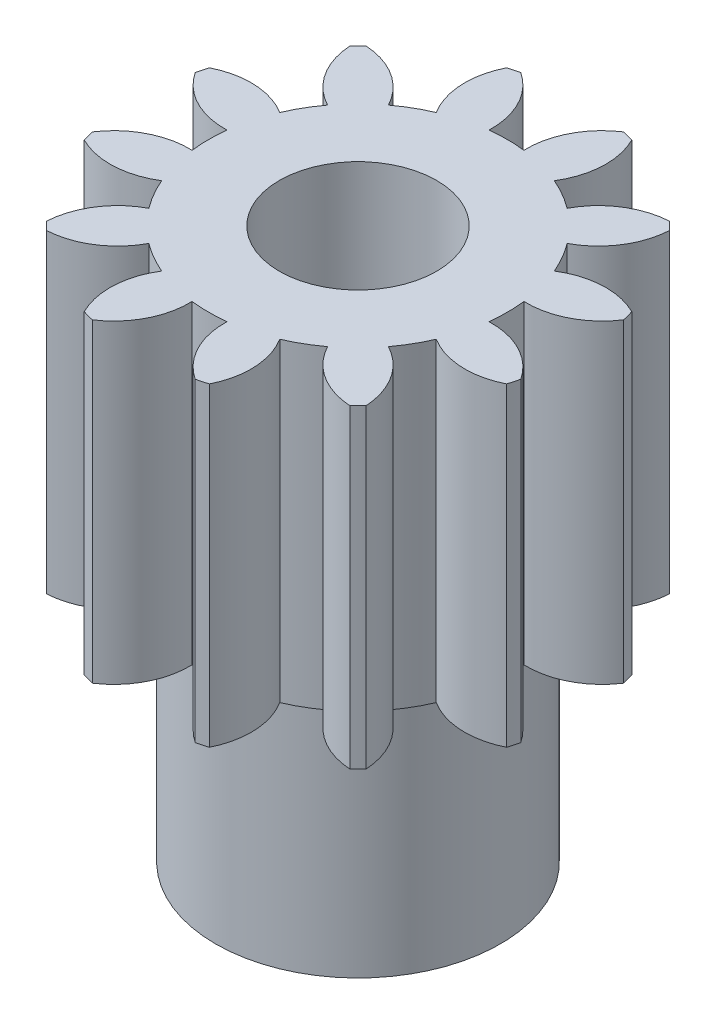
SolidWorks part; units mm, degrees
ref_plane "Front Plane" through (0, 0, 0) normal (0, 0, 1) x (1, 0, 0)
ref_plane "Top Plane" through (0, 0, 0) normal (0, 1, 0) x (1, 0, 0)
ref_plane "Right Plane" through (0, 0, 0) normal (1, 0, 0) x (0, 0, -1)
sketch "Sketch1" plane through (0, 0, 0) normal (0, 1, 0) x (1, 0, 0)
  circle A0 centre (0, 0) radius 17
  dimension "D1" = 34
extrude "Boss-Extrude1" add sketch "Sketch1" along normal blind 20
extrude "Cut-Extrude1" cut sketch "Sketch2" against normal blind 15
sketch "Sketch2" plane through (-13.8182, 15, -17.4966) normal (0, 1, 0) x (1, 0, 0)
  circle A0 centre (13.8182, -17.4966) radius 17
  arc A96 (19.498, -25.1104) -> (23.4557, -27.6513) centre (23.7376, -22.8596) ccw
  arc A97 (23.4557, -27.6513) -> (23.973, -27.1341) centre (13.8182, -17.4966) ccw
  arc A98 (23.973, -27.1341) -> (21.4321, -23.1764) centre (19.1813, -27.4159) ccw
  arc A99 (21.4321, -23.1764) -> (22.544, -21.2505) centre (13.8182, -17.4966) ccw
  arc A100 (22.544, -21.2505) -> (27.2419, -21.4721) centre (25.0902, -17.1814) ccw
  arc A101 (27.2419, -21.4721) -> (27.4313, -20.7655) centre (13.8182, -17.4966) ccw
  arc A102 (27.4313, -20.7655) -> (23.2519, -18.6085) centre (23.4224, -23.4055) ccw
  arc A103 (23.2519, -18.6085) -> (23.2519, -16.3847) centre (13.8182, -17.4966) ccw
  arc A104 (23.2519, -16.3847) -> (27.4313, -14.2276) centre (23.4224, -11.5877) ccw
  arc A105 (27.4313, -14.2276) -> (27.2419, -13.5211) centre (13.8182, -17.4966) ccw
  arc A106 (27.2419, -13.5211) -> (22.544, -13.7427) centre (25.0902, -17.8117) ccw
  arc A107 (22.544, -13.7427) -> (21.4321, -11.8168) centre (13.8182, -17.4966) ccw
  arc A108 (21.4321, -11.8168) -> (23.973, -7.8591) centre (19.1813, -7.5772) ccw
  arc A109 (23.973, -7.8591) -> (23.4557, -7.3418) centre (13.8182, -17.4966) ccw
  arc A110 (23.4557, -7.3418) -> (19.498, -9.8827) centre (23.7376, -12.1336) ccw
  arc A111 (19.498, -9.8827) -> (17.5722, -8.7708) centre (13.8182, -17.4966) ccw
  arc A112 (17.5722, -8.7708) -> (17.7938, -4.0729) centre (13.5031, -6.2247) ccw
  arc A113 (17.7938, -4.0729) -> (17.0872, -3.8836) centre (13.8182, -17.4966) ccw
  arc A114 (17.0872, -3.8836) -> (14.9302, -8.0629) centre (19.7271, -7.8924) ccw
  arc A115 (14.9302, -8.0629) -> (12.7063, -8.0629) centre (13.8182, -17.4966) ccw
  arc A116 (12.7063, -8.0629) -> (10.5493, -3.8836) centre (7.9094, -7.8924) ccw
  arc A117 (10.5493, -3.8836) -> (9.8427, -4.0729) centre (13.8182, -17.4966) ccw
  arc A118 (9.8427, -4.0729) -> (10.0643, -8.7708) centre (14.1334, -6.2247) ccw
  arc A119 (10.0643, -8.7708) -> (8.1385, -9.8827) centre (13.8182, -17.4966) ccw
  arc A120 (8.1385, -9.8827) -> (4.1808, -7.3418) centre (3.8989, -12.1336) ccw
  arc A121 (4.1808, -7.3418) -> (3.6635, -7.8591) centre (13.8182, -17.4966) ccw
  arc A122 (3.6635, -7.8591) -> (6.2044, -11.8168) centre (8.4552, -7.5772) ccw
  arc A123 (6.2044, -11.8168) -> (5.0925, -13.7427) centre (13.8182, -17.4966) ccw
  arc A124 (5.0925, -13.7427) -> (0.3946, -13.5211) centre (2.5463, -17.8117) ccw
  arc A125 (0.3946, -13.5211) -> (0.2052, -14.2276) centre (13.8182, -17.4966) ccw
  arc A126 (0.2052, -14.2276) -> (4.3845, -16.3847) centre (4.2141, -11.5877) ccw
  arc A127 (4.3845, -16.3847) -> (4.3845, -18.6085) centre (13.8182, -17.4966) ccw
  arc A128 (4.3845, -18.6085) -> (0.2052, -20.7655) centre (4.2141, -23.4055) ccw
  arc A129 (0.2052, -20.7655) -> (0.3946, -21.4721) centre (13.8182, -17.4966) ccw
  arc A130 (0.3946, -21.4721) -> (5.0925, -21.2505) centre (2.5463, -17.1814) ccw
  arc A131 (5.0925, -21.2505) -> (6.2044, -23.1764) centre (13.8182, -17.4966) ccw
  arc A132 (6.2044, -23.1764) -> (3.6635, -27.1341) centre (8.4552, -27.4159) ccw
  arc A133 (3.6635, -27.1341) -> (4.1808, -27.6513) centre (13.8182, -17.4966) ccw
  arc A134 (4.1808, -27.6513) -> (8.1385, -25.1104) centre (3.8989, -22.8596) ccw
  arc A135 (8.1385, -25.1104) -> (10.0643, -26.2224) centre (13.8182, -17.4966) ccw
  arc A136 (10.0643, -26.2224) -> (9.8427, -30.9203) centre (14.1334, -28.7685) ccw
  arc A137 (9.8427, -30.9203) -> (10.5493, -31.1096) centre (13.8182, -17.4966) ccw
  arc A138 (10.5493, -31.1096) -> (12.7063, -26.9303) centre (7.9094, -27.1008) ccw
  arc A139 (12.7063, -26.9303) -> (14.9302, -26.9303) centre (13.8182, -17.4966) ccw
  arc A140 (14.9302, -26.9303) -> (17.0872, -31.1096) centre (19.7271, -27.1008) ccw
  arc A141 (17.0872, -31.1096) -> (17.7938, -30.9203) centre (13.8182, -17.4966) ccw
  arc A142 (17.7938, -30.9203) -> (17.5722, -26.2224) centre (13.5031, -28.7685) ccw
  arc A143 (17.5722, -26.2224) -> (19.498, -25.1104) centre (13.8182, -17.4966) ccw
sketch "Sketch4" plane through (0, 15, 0) normal (0, -1, 0) x (1, 0, 0)
  circle A1 centre (0, 0) radius 17
  circle A2 centre (0, 0) radius 17
  arc A50 (5.6798, 7.6139) -> (3.7539, 8.7258) centre (0, 0) ccw
  arc A51 (3.7539, 8.7258) -> (3.9755, 13.4237) centre (-0.3151, 11.2719) ccw
  arc A52 (3.9755, 13.4237) -> (3.2689, 13.613) centre (0, 0) ccw
  arc A53 (3.2689, 13.613) -> (1.1119, 9.4337) centre (5.9089, 9.6042) ccw
  arc A54 (1.1119, 9.4337) -> (-1.1119, 9.4337) centre (0, 0) ccw
  arc A55 (-1.1119, 9.4337) -> (-3.2689, 13.613) centre (-5.9089, 9.6042) ccw
  arc A56 (-3.2689, 13.613) -> (-3.9755, 13.4237) centre (0, 0) ccw
  arc A57 (-3.9755, 13.4237) -> (-3.7539, 8.7258) centre (0.3151, 11.2719) ccw
  arc A58 (-3.7539, 8.7258) -> (-5.6798, 7.6139) centre (0, 0) ccw
  arc A59 (-5.6798, 7.6139) -> (-9.6375, 10.1547) centre (-9.9193, 5.363) ccw
  arc A60 (-9.6375, 10.1547) -> (-10.1547, 9.6375) centre (0, 0) ccw
  arc A61 (-10.1547, 9.6375) -> (-7.6139, 5.6798) centre (-5.363, 9.9193) ccw
  arc A62 (-7.6139, 5.6798) -> (-8.7258, 3.7539) centre (0, 0) ccw
  arc A63 (-8.7258, 3.7539) -> (-13.4237, 3.9755) centre (-11.2719, -0.3151) ccw
  arc A64 (-13.4237, 3.9755) -> (-13.613, 3.2689) centre (0, 0) ccw
  arc A65 (-13.613, 3.2689) -> (-9.4337, 1.1119) centre (-9.6042, 5.9089) ccw
  arc A66 (-9.4337, 1.1119) -> (-9.4337, -1.1119) centre (0, 0) ccw
  arc A67 (-9.4337, -1.1119) -> (-13.613, -3.2689) centre (-9.6042, -5.9089) ccw
  arc A68 (-13.613, -3.2689) -> (-13.4237, -3.9755) centre (0, 0) ccw
  arc A69 (-13.4237, -3.9755) -> (-8.7258, -3.7539) centre (-11.2719, 0.3151) ccw
  arc A70 (-8.7258, -3.7539) -> (-7.6139, -5.6798) centre (0, 0) ccw
  arc A71 (-7.6139, -5.6798) -> (-10.1547, -9.6375) centre (-5.363, -9.9193) ccw
  arc A72 (-10.1547, -9.6375) -> (-9.6375, -10.1547) centre (0, 0) ccw
  arc A73 (-9.6375, -10.1547) -> (-5.6798, -7.6139) centre (-9.9193, -5.363) ccw
  arc A74 (-5.6798, -7.6139) -> (-3.7539, -8.7258) centre (0, 0) ccw
  arc A75 (-3.7539, -8.7258) -> (-3.9755, -13.4237) centre (0.3151, -11.2719) ccw
  arc A76 (-3.9755, -13.4237) -> (-3.2689, -13.613) centre (0, 0) ccw
  arc A77 (-3.2689, -13.613) -> (-1.1119, -9.4337) centre (-5.9089, -9.6042) ccw
  arc A78 (-1.1119, -9.4337) -> (1.1119, -9.4337) centre (0, 0) ccw
  arc A79 (1.1119, -9.4337) -> (3.2689, -13.613) centre (5.9089, -9.6042) ccw
  arc A80 (3.2689, -13.613) -> (3.9755, -13.4237) centre (0, 0) ccw
  arc A81 (3.9755, -13.4237) -> (3.7539, -8.7258) centre (-0.3151, -11.2719) ccw
  arc A82 (3.7539, -8.7258) -> (5.6798, -7.6139) centre (0, 0) ccw
  arc A83 (5.6798, -7.6139) -> (9.6375, -10.1547) centre (9.9193, -5.363) ccw
  arc A84 (9.6375, -10.1547) -> (10.1547, -9.6375) centre (0, 0) ccw
  arc A85 (10.1547, -9.6375) -> (7.6139, -5.6798) centre (5.363, -9.9193) ccw
  arc A86 (7.6139, -5.6798) -> (8.7258, -3.7539) centre (0, 0) ccw
  arc A87 (8.7258, -3.7539) -> (13.4237, -3.9755) centre (11.2719, 0.3151) ccw
  arc A88 (13.4237, -3.9755) -> (13.613, -3.2689) centre (0, 0) ccw
  arc A89 (13.613, -3.2689) -> (9.4337, -1.1119) centre (9.6042, -5.9089) ccw
  arc A90 (9.4337, -1.1119) -> (9.4337, 1.1119) centre (0, 0) ccw
  arc A91 (9.4337, 1.1119) -> (13.613, 3.2689) centre (9.6042, 5.9089) ccw
  arc A92 (13.613, 3.2689) -> (13.4237, 3.9755) centre (0, 0) ccw
  arc A93 (13.4237, 3.9755) -> (8.7258, 3.7539) centre (11.2719, -0.3151) ccw
  arc A94 (8.7258, 3.7539) -> (7.6139, 5.6798) centre (0, 0) ccw
  arc A95 (7.6139, 5.6798) -> (10.1547, 9.6375) centre (5.363, 9.9193) ccw
  arc A96 (10.1547, 9.6375) -> (9.6375, 10.1547) centre (0, 0) ccw
  arc A97 (9.6375, 10.1547) -> (5.6798, 7.6139) centre (9.9193, 5.363) ccw
  arc A98 (5.6798, 7.6139) -> (3.7539, 8.7258) centre (0, 0) ccw
  arc A99 (3.7539, 8.7258) -> (3.9755, 13.4237) centre (-0.3151, 11.2719) ccw
  arc A100 (3.9755, 13.4237) -> (3.2689, 13.613) centre (0, 0) ccw
  arc A101 (3.2689, 13.613) -> (1.1119, 9.4337) centre (5.9089, 9.6042) ccw
  arc A102 (1.1119, 9.4337) -> (-1.1119, 9.4337) centre (0, 0) ccw
  arc A103 (-1.1119, 9.4337) -> (-3.2689, 13.613) centre (-5.9089, 9.6042) ccw
  arc A104 (-3.2689, 13.613) -> (-3.9755, 13.4237) centre (0, 0) ccw
  arc A105 (-3.9755, 13.4237) -> (-3.7539, 8.7258) centre (0.3151, 11.2719) ccw
  arc A106 (-3.7539, 8.7258) -> (-5.6798, 7.6139) centre (0, 0) ccw
  arc A107 (-5.6798, 7.6139) -> (-9.6375, 10.1547) centre (-9.9193, 5.363) ccw
  arc A108 (-9.6375, 10.1547) -> (-10.1547, 9.6375) centre (0, 0) ccw
  arc A109 (-10.1547, 9.6375) -> (-7.6139, 5.6798) centre (-5.363, 9.9193) ccw
  arc A110 (-7.6139, 5.6798) -> (-8.7258, 3.7539) centre (0, 0) ccw
  arc A111 (-8.7258, 3.7539) -> (-13.4237, 3.9755) centre (-11.2719, -0.3151) ccw
  arc A112 (-13.4237, 3.9755) -> (-13.613, 3.2689) centre (0, 0) ccw
  arc A113 (-13.613, 3.2689) -> (-9.4337, 1.1119) centre (-9.6042, 5.9089) ccw
  arc A114 (-9.4337, 1.1119) -> (-9.4337, -1.1119) centre (0, 0) ccw
  arc A115 (-9.4337, -1.1119) -> (-13.613, -3.2689) centre (-9.6042, -5.9089) ccw
  arc A116 (-13.613, -3.2689) -> (-13.4237, -3.9755) centre (0, 0) ccw
  arc A117 (-13.4237, -3.9755) -> (-8.7258, -3.7539) centre (-11.2719, 0.3151) ccw
  arc A118 (-8.7258, -3.7539) -> (-7.6139, -5.6798) centre (0, 0) ccw
  arc A119 (-7.6139, -5.6798) -> (-10.1547, -9.6375) centre (-5.363, -9.9193) ccw
  arc A120 (-10.1547, -9.6375) -> (-9.6375, -10.1547) centre (0, 0) ccw
  arc A121 (-9.6375, -10.1547) -> (-5.6798, -7.6139) centre (-9.9193, -5.363) ccw
  arc A122 (-5.6798, -7.6139) -> (-3.7539, -8.7258) centre (0, 0) ccw
  arc A123 (-3.7539, -8.7258) -> (-3.9755, -13.4237) centre (0.3151, -11.2719) ccw
  arc A124 (-3.9755, -13.4237) -> (-3.2689, -13.613) centre (0, 0) ccw
  arc A125 (-3.2689, -13.613) -> (-1.1119, -9.4337) centre (-5.9089, -9.6042) ccw
  arc A126 (-1.1119, -9.4337) -> (1.1119, -9.4337) centre (0, 0) ccw
  arc A127 (1.1119, -9.4337) -> (3.2689, -13.613) centre (5.9089, -9.6042) ccw
  arc A128 (3.2689, -13.613) -> (3.9755, -13.4237) centre (0, 0) ccw
  arc A129 (3.9755, -13.4237) -> (3.7539, -8.7258) centre (-0.3151, -11.2719) ccw
  arc A130 (3.7539, -8.7258) -> (5.6798, -7.6139) centre (0, 0) ccw
  arc A131 (5.6798, -7.6139) -> (9.6375, -10.1547) centre (9.9193, -5.363) ccw
  arc A132 (9.6375, -10.1547) -> (10.1547, -9.6375) centre (0, 0) ccw
  arc A133 (10.1547, -9.6375) -> (7.6139, -5.6798) centre (5.363, -9.9193) ccw
  arc A134 (7.6139, -5.6798) -> (8.7258, -3.7539) centre (0, 0) ccw
  arc A135 (8.7258, -3.7539) -> (13.4237, -3.9755) centre (11.2719, 0.3151) ccw
  arc A136 (13.4237, -3.9755) -> (13.613, -3.2689) centre (0, 0) ccw
  arc A137 (13.613, -3.2689) -> (9.4337, -1.1119) centre (9.6042, -5.9089) ccw
  arc A138 (9.4337, -1.1119) -> (9.4337, 1.1119) centre (0, 0) ccw
  arc A139 (9.4337, 1.1119) -> (13.613, 3.2689) centre (9.6042, 5.9089) ccw
  arc A140 (13.613, 3.2689) -> (13.4237, 3.9755) centre (0, 0) ccw
  arc A141 (13.4237, 3.9755) -> (8.7258, 3.7539) centre (11.2719, -0.3151) ccw
  arc A142 (8.7258, 3.7539) -> (7.6139, 5.6798) centre (0, 0) ccw
  arc A143 (7.6139, 5.6798) -> (10.1547, 9.6375) centre (5.363, 9.9193) ccw
  arc A144 (10.1547, 9.6375) -> (9.6375, 10.1547) centre (0, 0) ccw
  arc A145 (9.6375, 10.1547) -> (5.6798, 7.6139) centre (9.9193, 5.363) ccw
  dimension "D1" = 0
  dimension "D2" = 0
extrude "Cut-Extrude2" cut sketch "Sketch4" against normal up to surface (5 mm away) up to face at (0, 20, 17)
sketch "Sketch5" plane through (0, 0, 0) normal (0, -1, 0) x (1, 0, 0)
  circle A0 centre (0, 0) radius 9.05
  dimension "D1" = 18.1
extrude "Boss-Extrude2" add sketch "Sketch5" along normal blind 15
sketch "Sketch6" plane through (0, -15, 0) normal (0, -1, 0) x (1, 0, 0)
  circle A0 centre (0, 0) radius 5
  dimension "D1" = 10
extrude "Cut-Extrude3" cut sketch "Sketch6" against normal up to surface (35 mm away) up to face at (0, 20, 0)
